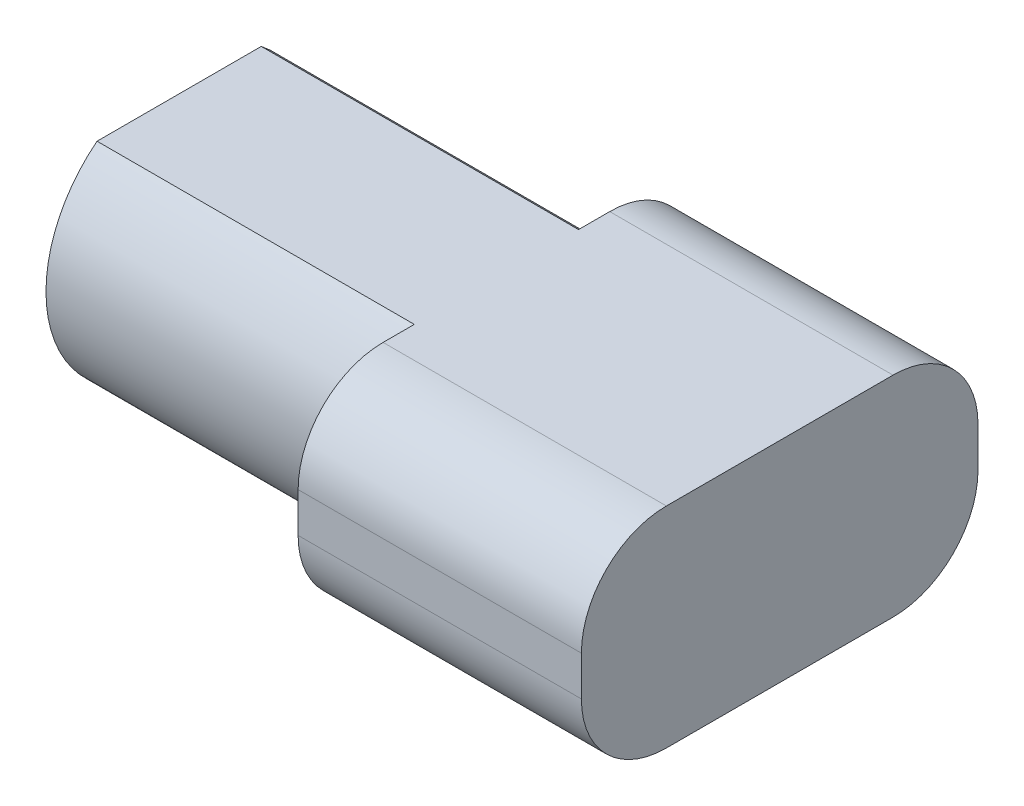
SolidWorks part; units mm, degrees
ref_plane "Front Plane" through (0, 0, 0) normal (0, 0, 1) x (1, 0, 0)
ref_plane "Top Plane" through (0, 0, 0) normal (0, 1, 0) x (1, 0, 0)
ref_plane "Right Plane" through (0, 0, 0) normal (1, 0, 0) x (0, 0, -1)
sketch "Sketch1" plane through (0, 0, 0) normal (1, 0, 0) x (0, 0, -1)
  line L0 (-1.4491, 1.85) -> (1.4491, 1.85)
  line L5 (-1.4491, -1.85) -> (1.4491, -1.85)
  arc A2 (1.4491, -1.85) -> (1.4491, 1.85) centre (0, 0) ccw
  arc A3 (-1.4491, 1.85) -> (-1.4491, -1.85) centre (0, 0) ccw
extrude "Boss-Extrude1" add sketch "Sketch1" along normal blind 5.6
sketch "Sketch2" plane through (5.6, 0, 0) normal (1, 0, 0) x (0, 0, -1)
  line L0 (0, 1.85) -> (-3.5, 1.85)
  line L1 (1.4491, 1.85) -> (-1.4491, 1.85) construction
  line L2 (0, 1.85) -> (3.5, 1.85)
  line L3 (-1.4491, -1.85) -> (1.4491, -1.85) construction
  line L4 (-1.4491, -1.85) -> (1.4491, -1.85)
  line L5 (-3.5, 1.85) -> (-3.5, -1.85)
  line L6 (-3.5, -1.85) -> (-1.4491, -1.85)
  line L7 (1.4491, -1.85) -> (3.5, -1.85)
  line L8 (3.5, -1.85) -> (3.5, 1.85)
extrude "Boss-Extrude2" add sketch "Sketch2" along normal blind 5
fillet "Fillet1" radius 1.5 4 edges at (8.1, -1.85, -3.5) (8.1, 1.85, -3.5) (8.1, -1.85, 3.5) (8.1, 1.85, 3.5)
